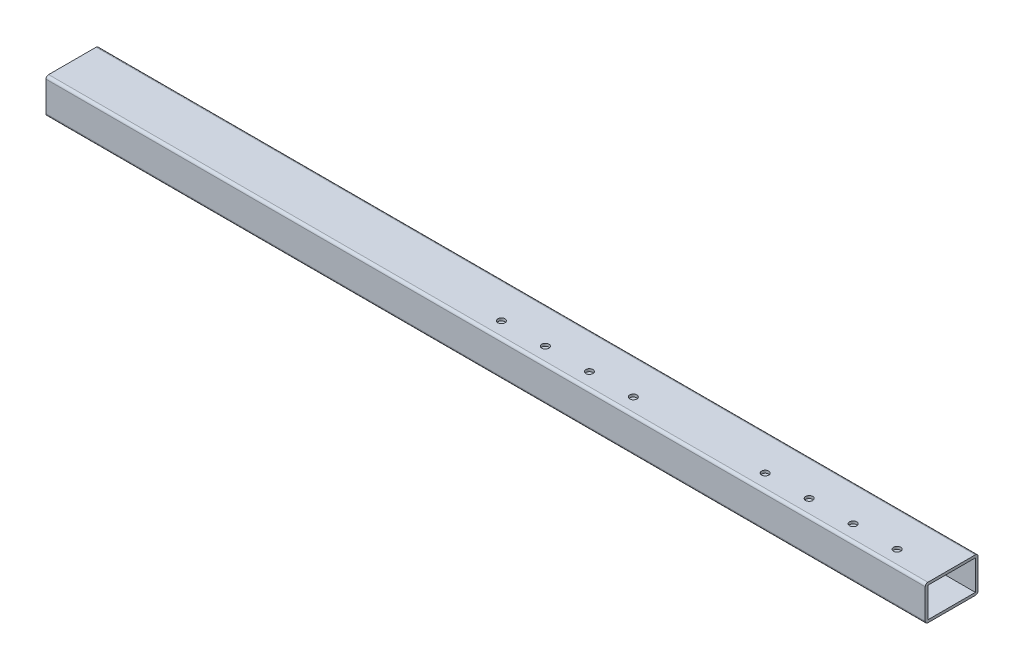
SolidWorks part; units mm, degrees
ref_plane "Спереди" through (0, 0, 0) normal (0, 0, 1) x (1, 0, 0)
ref_plane "Сверху" through (0, 0, 0) normal (0, 1, 0) x (1, 0, 0)
ref_plane "Справа" through (0, 0, 0) normal (1, 0, 0) x (0, 0, -1)
sketch "Эскиз1" plane through (0, 0, 0) normal (1, 0, 0) x (0, 0, -1)
  line L1 (-27, 20) -> (27, 20)
  line L2 (-30, 17) -> (-30, -17)
  line L3 (-27, -20) -> (27, -20)
  line L4 (30, 17) -> (30, -17)
  line L5 (-30, 20) -> (30, -20) construction
  line L6 (-30, -20) -> (30, 20) construction
  arc A0 (-27, 20) -> (-30, 17) centre (-27, 17) ccw
  arc A1 (-30, -17) -> (-27, -20) centre (-27, -17) ccw
  arc A2 (27, -20) -> (30, -17) centre (27, -17) ccw
  arc A3 (27, 20) -> (30, 17) centre (27, 17) cw
  point P0 (0, 0)
  dimension "D1" = 3
extrude "Вытянуть-Тонкостенный1" add sketch "Эскиз1" along normal blind 1000 thin
sketch "Эскиз2" plane through (0, 20, 0) normal (0, 1, 0) x (1, 0, 0)
  circle A0 centre (950, -12) radius 4.05
  circle A1 centre (900, -12) radius 4.05
  circle A2 centre (850, -12) radius 4.05
  circle A3 centre (800, -12) radius 4.05
  circle A4 centre (650, -12) radius 4.05
  circle A5 centre (600, -12) radius 4.05
  circle A6 centre (550, -12) radius 4.05
  circle A7 centre (500, -12) radius 4.05
  point P3 (0, 0)
  dimension "D1" = 4
  dimension "D2" = 2
extrude "Вырез-Вытянуть1" cut sketch "Эскиз2" against normal through all
